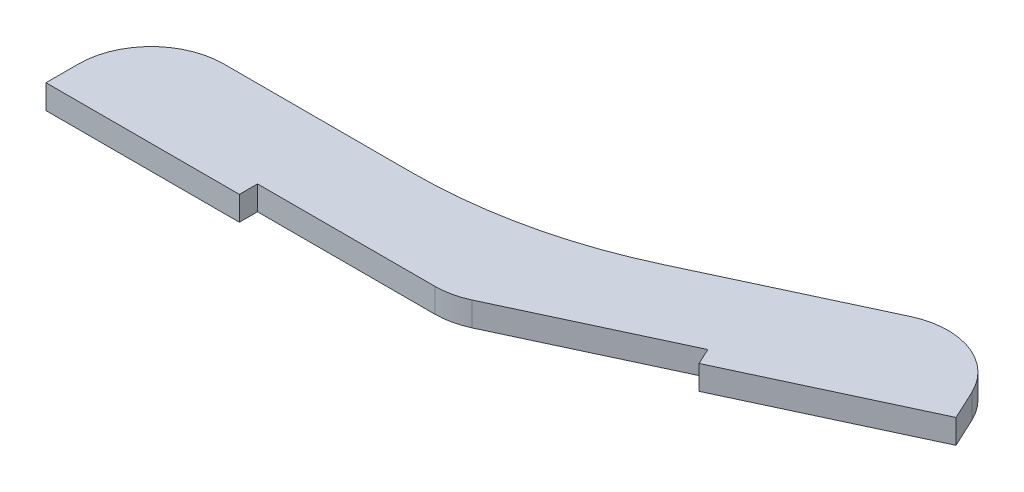
SolidWorks part; units mm, degrees
material "Plain Carbon Steel"
ref_plane "Front Plane" through (0, 0, 0) normal (0, 0, 1) x (1, 0, 0)
ref_plane "Top Plane" through (0, 0, 0) normal (0, 1, 0) x (1, 0, 0)
ref_plane "Right Plane" through (0, 0, 0) normal (1, 0, 0) x (0, 0, -1)
sketch "Sketch1" plane through (0, 0, 0) normal (0, 1, 0) x (1, 0, 0)
  line L0 (-50.8, 0) -> (0, 0)
  line L1 (0, 0) -> (46.0404, 21.469)
  line L2 (-50.8, 0) -> (-50.8, 12.7)
  line L3 (-50.8, 12.7) -> (40.6732, 32.9791)
  line L4 (40.6732, 32.9791) -> (46.0404, 21.469)
  dimension "D1" = 50.8
  dimension "D2" = 50.8
  dimension "D3" = 25
  dimension "D4" = 12.7
extrude "Boss-Extrude1" add sketch "Sketch1" along normal blind 3.175
sketch "Sketch2" plane through (0, 3.175, 0) normal (0, 1, 0) x (1, 0, 0)
  line L0 (23.0202, 10.7345) -> (46.0404, 21.469)
  line L1 (-50.8, 0) -> (-25.4, 0)
  line L2 (-50.8, 0) -> (-50.8, -2.3813)
  line L3 (-50.8, -2.3813) -> (-25.4, -2.3813)
  line L4 (-25.4, 0) -> (-25.4, -2.3813)
  line L5 (0, 0) -> (46.0404, 21.469) construction
  line L6 (46.0404, 21.469) -> (47.0468, 19.3109)
  line L7 (47.0468, 19.3109) -> (24.0266, 8.5764)
  line L8 (24.0266, 8.5764) -> (23.0202, 10.7345)
  dimension "D1" = 2.3813
extrude "Boss-Extrude2" add sketch "Sketch2" against normal up to surface (3.175 mm away) up to face at (-2.9773, 0, -13.4296)
sketch "Sketch3" plane through (0, 3.175, 0) normal (0, 1, 0) x (1, 0, 0)
  line L3 (-25.4, 11.43) -> (-50.8, 11.43)
  line L4 (-50.8, 12.7) -> (-50.8, -2.3813) construction
  line L5 (-2.534, 11.43) -> (18.1897, 21.0936)
  line L6 (-25.4, 11.43) -> (-2.534, 11.43)
  line L7 (-2.534, 11.43) -> (18.1897, 21.0936)
  line L8 (-25.4, 11.43) -> (-2.534, 11.43)
  line L9 (-50.8, 11.43) -> (-50.8, 12.7)
  line L10 (-50.8, 12.7) -> (40.6732, 32.9791)
  line L11 (18.1897, 21.0936) -> (41.2099, 31.8281)
  line L12 (47.0468, 19.3109) -> (40.6732, 32.9791) construction
  line L13 (41.2099, 31.8281) -> (40.6732, 32.9791)
  dimension "D1" = 11.43
extrude "Cut-Extrude1" cut sketch "Sketch3" against normal through all
fillet "Fillet1" radius 9.525 3 edges at (0, 1.5875, 0) (41.2099, 1.5875, -31.8281) (-50.8, 1.5875, -11.43)
fillet "Fillet2" radius 63.5 1 edges
